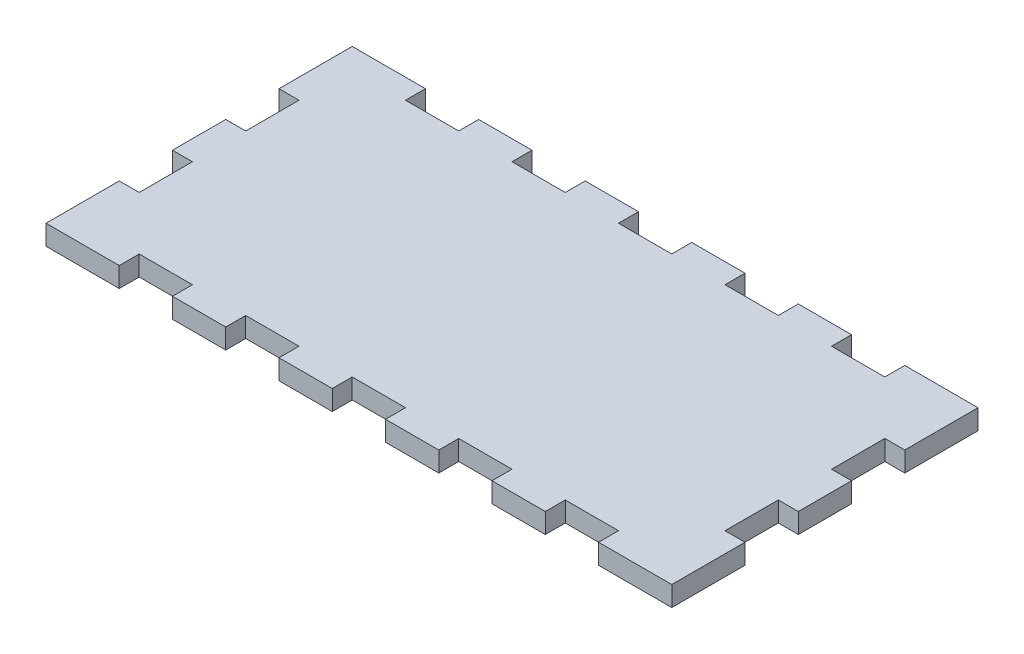
SolidWorks part; units mm, degrees
ref_plane "Front Plane" through (0, 0, 0) normal (0, 0, 1) x (1, 0, 0)
ref_plane "Top Plane" through (0, 0, 0) normal (0, 1, 0) x (1, 0, 0)
ref_plane "Right Plane" through (0, 0, 0) normal (1, 0, 0) x (0, 0, -1)
sketch "Sketch2" plane through (0, 0, 0) normal (0, 1, 0) x (1, 0, 0)
  line L1 (139.7, -63.5) -> (-139.7, -63.5)
  line L2 (139.7, -63.5) -> (139.7, 63.5)
  line L3 (139.7, 63.5) -> (-139.7, 63.5)
  line L4 (-139.7, -63.5) -> (-139.7, 63.5)
  line L5 (139.7, -63.5) -> (-139.7, 63.5) construction
  line L6 (139.7, 63.5) -> (-139.7, -63.5) construction
  point P0 (0, 0)
  dimension "D1" = 279.4
  dimension "D2" = 127
extrude "Boss-Extrude1" add sketch "Sketch2" along normal blind 9.525
sketch "Sketch3" plane through (0, 0, 63.5) normal (0, 0, 1) x (1, 0, 0)
  line L0 (-139.7, 9.525) -> (139.7, 9.525) construction
  line L1 (-139.7, 0) -> (-114.3, 0)
  line L2 (-139.7, 0) -> (-139.7, 9.525)
  line L3 (-139.7, 9.525) -> (-114.3, 9.525)
  line L4 (-114.3, 0) -> (-114.3, 9.525)
  dimension "D1" = 25.4
extrude "Boss-Extrude2" add sketch "Sketch3" along normal blind 9.525
pattern_linear "LPattern1" count 6 spacing 50.8 along (1, 0, 0) of "Boss-Extrude2"
mirror "Mirror1" about plane through (0, 0, 0) normal (0, 0, 1) of "LPattern1", "Boss-Extrude2"
sketch "Sketch4" plane through (139.7, 0, 0) normal (1, 0, 0) x (0, 0, -1)
  line L0 (-73.025, 0) -> (73.025, 0) construction
  line L1 (-63.5, 0) -> (-38.1, 0)
  line L2 (-63.5, 0) -> (-63.5, 9.525)
  line L3 (-63.5, 9.525) -> (-38.1, 9.525)
  line L4 (-38.1, 0) -> (-38.1, 9.525)
  line L5 (-73.025, 9.525) -> (73.025, 9.525) construction
  line L6 (-73.025, 0) -> (-73.025, 9.525) construction
  dimension "D1" = 9.525
  dimension "D2" = 25.4
extrude "Boss-Extrude3" add sketch "Sketch4" along normal blind 9.525
pattern_linear "LPattern2" count 3 spacing 50.8 along (0, 0, -1) of "Boss-Extrude3"
mirror "Mirror2" about plane through (0, 0, 0) normal (1, 0, 0) of "LPattern2", "Boss-Extrude3"
sketch "Sketch6" plane through (0, 0, 63.5) normal (0, 0, 1) x (1, 0, 0)
  line L1 (149.225, 9.525) -> (139.7, 9.525)
  line L2 (149.225, 9.525) -> (149.225, 0)
  line L3 (149.225, 0) -> (139.7, 0)
  line L4 (139.7, 9.525) -> (139.7, 0)
extrude "Boss-Extrude4" add sketch "Sketch6" along normal blind 9.525
mirror "Mirror3" about plane through (0, 0, 0) normal (1, 0, 0) of "Boss-Extrude4"
mirror "Mirror4" about plane through (0, 0, 0) normal (0, 0, 1) of "Mirror3"
sketch "Sketch7" plane through (0, 9.525, 0) normal (0, 1, 0) x (1, 0, 0)
  circle A0 centre (-29.2864, 23.8119) radius 0.032
  circle A1 centre (-23.072, 14.7922) radius 0.1056
  circle A2 centre (27.5, 22.9863) radius 2
  circle A3 centre (22.5, 12.9863) radius 2
extrude "Cut-Extrude1" [suppressed] cut sketch "Sketch7" against normal through all
sketch "Sketch8" plane through (0, 9.525, 0) normal (0, 1, 0) x (1, 0, 0)
  circle A0 centre (-25.974, 23.4033) radius 0.0509
  circle A1 centre (-24.0521, 14.3728) radius 0.0812
  circle A2 centre (-27.5, -10.3679) radius 2
  circle A3 centre (-22.5, -20.3679) radius 2
extrude "Cut-Extrude3" [suppressed] cut sketch "Sketch8" against normal through all contours A2 A0 | A3
sketch "Sketch9" [suppressed] plane through (0, 0, 0) normal (0, -1, 0) x (1, 0, 0)
  circle A0 centre (-22.5, -12.9863) radius 3.81
  circle A1 centre (-27.5, -22.9863) radius 3.81
  circle A2 centre (22.5, -12.9863) radius 3.81
  circle A3 centre (27.5, -22.9863) radius 3.81
  dimension "D1" = 7.62
  dimension "D2" = 7.62
  dimension "D3" = 7.62
  dimension "D4" = 7.62
extrude "Cut-Extrude4" [suppressed] cut sketch "Sketch9" against normal blind 4.7625
